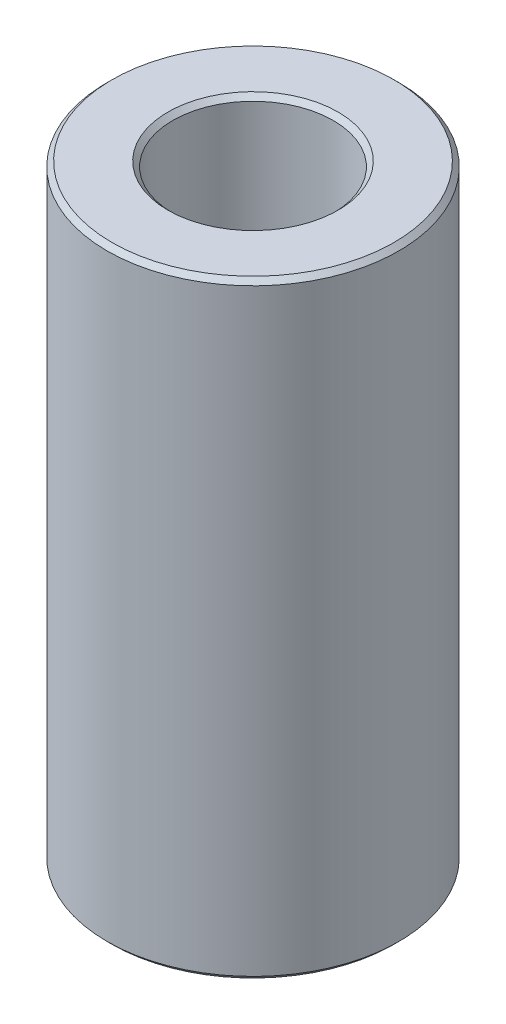
SolidWorks part; units mm, degrees
material "A5052"
ref_plane "Front Plane" through (0, 0, 0) normal (0, 0, 1) x (1, 0, 0)
ref_plane "Top Plane" through (0, 0, 0) normal (0, 1, 0) x (1, 0, 0)
ref_plane "Right Plane" through (0, 0, 0) normal (1, 0, 0) x (0, 0, -1)
sketch "Sketch1" plane through (0, 0, 0) normal (0, 1, 0) x (1, 0, 0)
  circle A0 centre (0, 0) radius 6
  dimension "D1" = 12
extrude "Boss-Extrude1" add sketch "Sketch1" along normal blind 25
hole_wizard "M6 Clearance Hole1" positions "Sketch2" profile "Sketch3" hole size "M6" standard "ANSI Metric" end condition through all
sketch "Sketch2" plane through (0, 25, 0) normal (0, 1, 0) x (1, 0, 0)
  point P0 (0, 0)
sketch "Sketch3" plane through (0, 25, 0) normal (1, 0, 0) x (0, 0, 1)
  line L0 (0, 0) -> (0, 25)
  line L1 (0, 25) -> (3.3, 25)
  line L2 (3.3, 25) -> (3.3, 0)
  line L5 (3.3, 0) -> (0, 0)
  line L11 (0, -6.35) -> (0, 107.95) construction
  dimension "Thru Hole Dia." = 6.6
  dimension "Thru Hole Depth" = 25
chamfer "Chamfer1" distance 0.2 angle 45 4 edges at (0, 0, 6) (0, 25, 6) (0, 0, 3.3) (0, 25, 3.3)
